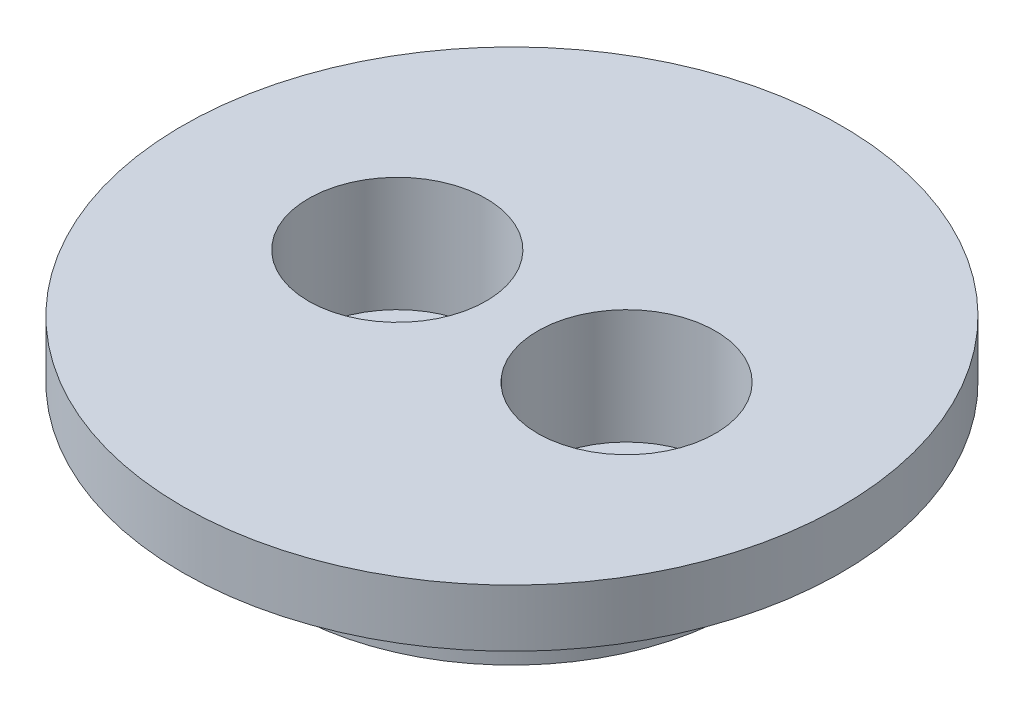
SolidWorks part; units mm, degrees
material "PET"
ref_plane "Front Plane" through (0, 0, 0) normal (0, 0, 1) x (1, 0, 0)
ref_plane "Top Plane" through (0, 0, 0) normal (0, 1, 0) x (1, 0, 0)
ref_plane "Right Plane" through (0, 0, 0) normal (1, 0, 0) x (0, 0, -1)
sketch "Sketch1" plane through (0, 35, 0) normal (0, 1, 0) x (1, 0, 0)
  circle A0 centre (0, 0) radius 7.85
  circle A1 centre (-4, 0) radius 1.5
  circle A2 centre (4, 0) radius 1.5
  dimension "D1" = 15.7
extrude "Boss-Extrude1" add sketch "Sketch1" along normal blind 3
sketch "Sketch2" plane through (0, 38, 0) normal (0, 1, 0) x (1, 0, 0)
  circle A0 centre (0, 0) radius 11.5
  circle A1 centre (-4, 0) radius 1.5
  circle A2 centre (4, 0) radius 1.5
  dimension "D1" = 23
extrude "Boss-Extrude2" add sketch "Sketch2" along normal blind 2
sketch "Sketch3" plane through (0, 40, 0) normal (0, 1, 0) x (1, 0, 0)
  circle A2 centre (-4, 0) radius 3.1
  circle A3 centre (-4, 0) radius 3.1
  circle A5 centre (4, 0) radius 3.1
  circle A6 centre (4, 0) radius 3.1
  dimension "D1" = 1.6
  dimension "D2" = 1.6
extrude "Cut-Extrude1" cut sketch "Sketch3" against normal blind 4
